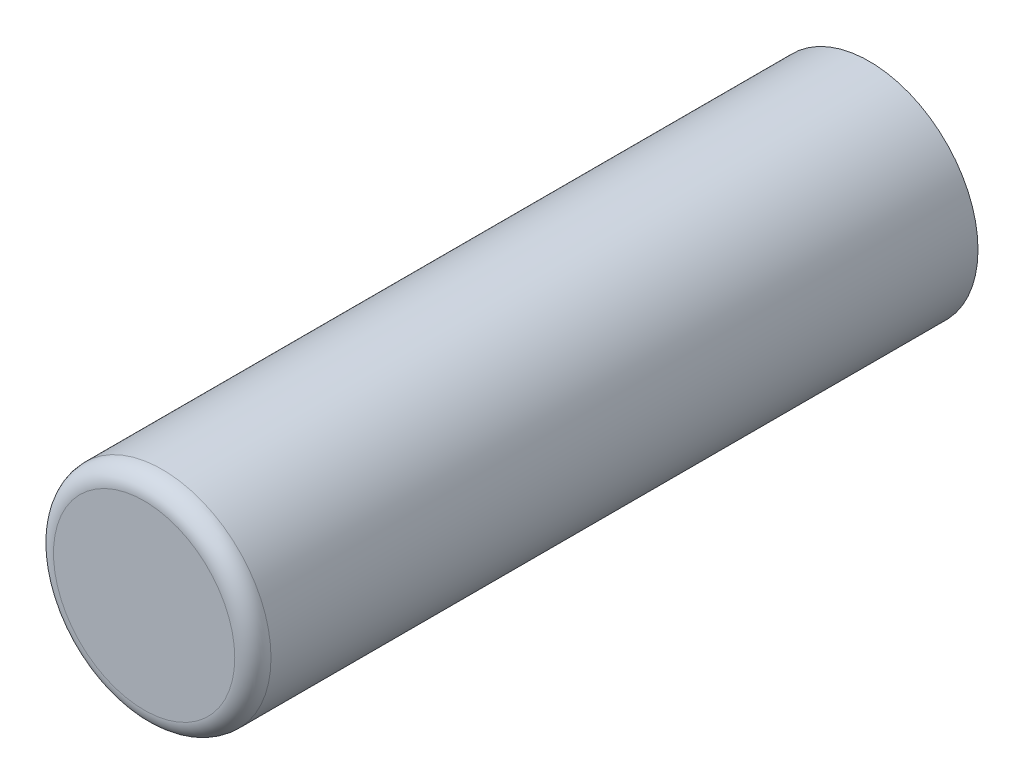
SolidWorks part; units mm, degrees
ref_plane "Front Plane" through (0, 0, 0) normal (0, 0, 1) x (1, 0, 0)
ref_plane "Top Plane" through (0, 0, 0) normal (0, 1, 0) x (1, 0, 0)
ref_plane "Right Plane" through (0, 0, 0) normal (1, 0, 0) x (0, 0, -1)
sketch "Sketch1" plane through (0, 0, 0) normal (0, 0, 1) x (1, 0, 0)
  circle A0 centre (0, 0) radius 4.8
  dimension "D1" = 9.6
extrude "Boss-Extrude1" add sketch "Sketch1" along normal mid plane 32
fillet "Fillet1" radius 0.8 1 edges at (4.8, 0, 16)
